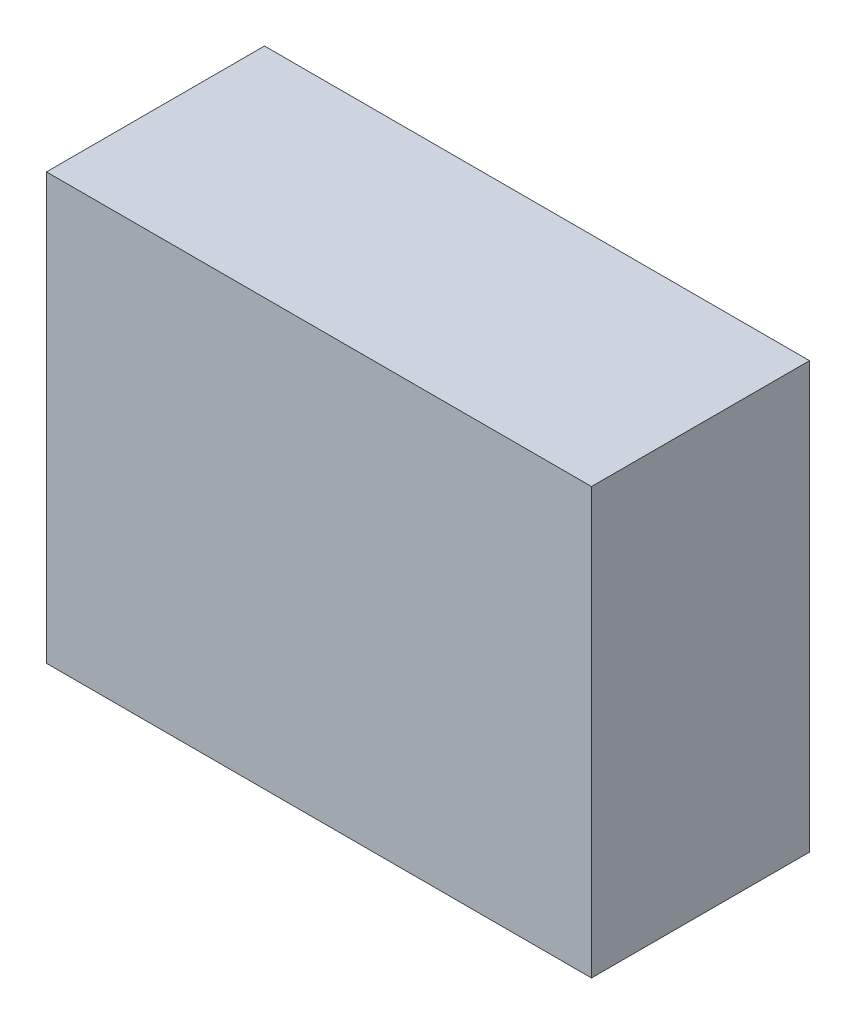
SolidWorks part; units mm, degrees
ref_plane "Front Plane" through (0, 0, 0) normal (0, 0, 1) x (1, 0, 0)
ref_plane "Top Plane" through (0, 0, 0) normal (0, 1, 0) x (1, 0, 0)
ref_plane "Right Plane" through (0, 0, 0) normal (1, 0, 0) x (0, 0, -1)
sketch "Sketch1" plane through (0, 0, 0) normal (1, 0, 0) x (0, 0, -1)
  line L1 (-2.1, -4.1) -> (2.1, -4.1)
  line L2 (-2.1, -4.1) -> (-2.1, 4.1)
  line L3 (-2.1, 4.1) -> (2.1, 4.1)
  line L4 (2.1, -4.1) -> (2.1, 4.1)
  line L5 (-2.1, -4.1) -> (2.1, 4.1) construction
  line L6 (-2.1, 4.1) -> (2.1, -4.1) construction
  point P0 (0, 0)
  dimension "D1" = 4.2
  dimension "D2" = 8.2
extrude "Boss-Extrude1" add sketch "Sketch1" along normal blind 10.5
